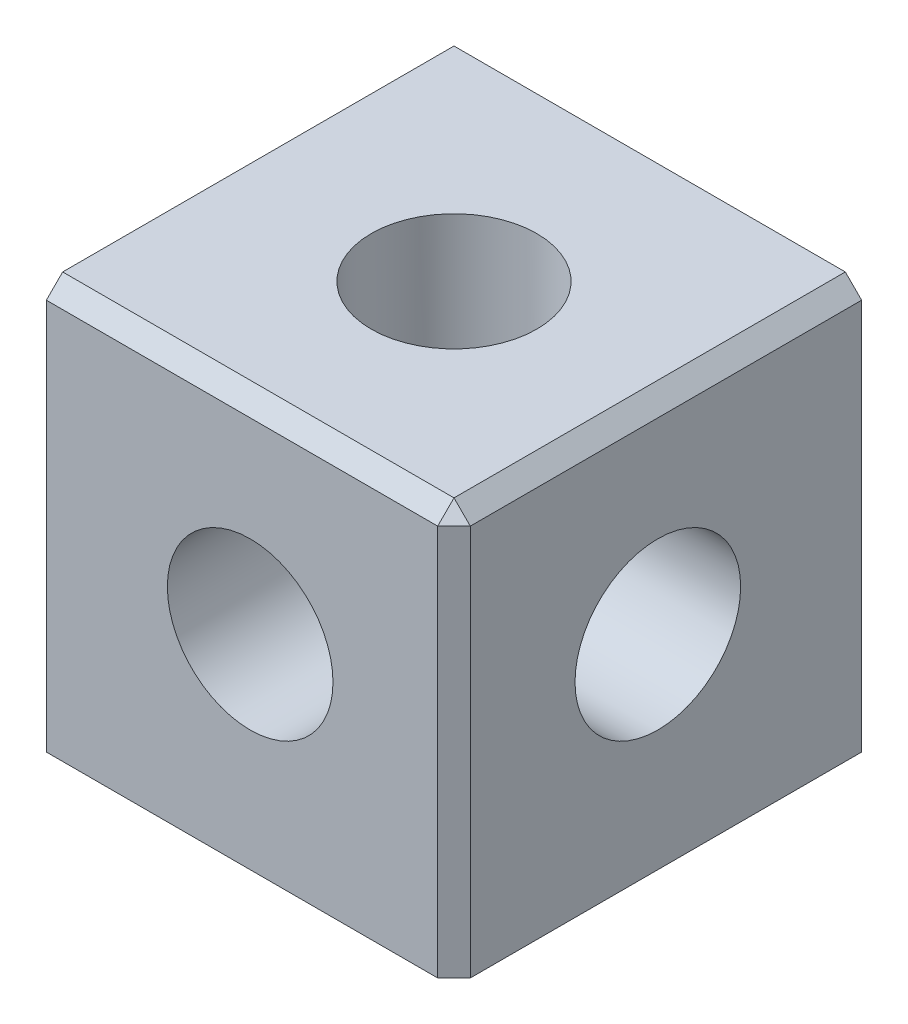
SolidWorks part; units mm, degrees
ref_plane "Front Plane" through (0, 0, 0) normal (0, 0, 1) x (1, 0, 0)
ref_plane "Top Plane" through (0, 0, 0) normal (0, 1, 0) x (1, 0, 0)
ref_plane "Right Plane" through (0, 0, 0) normal (1, 0, 0) x (0, 0, -1)
ref_plane "Plane1" through (0, 25.4, 0) normal (0, 1, 0) x (1, 0, 0)
sketch "Sketch1" plane through (0, 25.4, 0) normal (0, 1, 0) x (1, 0, 0)
  line L0 (-12.7, 12.7) -> (-12.7, -12.7)
  line L1 (-12.7, -12.7) -> (12.7, -12.7)
  line L2 (12.7, -12.7) -> (12.7, 12.7)
  line L3 (12.7, 12.7) -> (-12.7, 12.7)
extrude "Boss-Extrude1" add sketch "Sketch1" against normal blind 25.4
hole_wizard "Hole1" positions "Sketch3" profile "Sketch2" legacy
sketch "Sketch3" plane through (0, 0, 0) normal (0, -1, 0) x (-1, 0, 0)
  point P0 (0, 0)
sketch "Sketch2" plane through (0, 0, 0) normal (1, 0, 0) x (0, 0, -1)
  line L0 (0, 0) -> (0, 25.4)
  line L1 (0, 25.4) -> (5.16, 25.4)
  line L2 (5.16, 25.4) -> (5.16, 3.3)
  line L3 (5.16, 3.3) -> (3.26, 3.3)
  line L4 (3.26, 3.3) -> (3.26, 0)
  line L5 (3.26, 0) -> (0, 0)
  line L6 (0, 110) -> (0, -10) construction
  dimension "Diameter" = 10.32
  dimension "Depth" = 25.4
  dimension "C-Bore Diameter" = 6.52
  dimension "C-Bore Depth" = 3.3
hole_wizard "Hole2" positions "Sketch5" profile "Sketch4" legacy
sketch "Sketch5" plane through (0, 0, -12.7) normal (0, 0, -1) x (-1, 0, 0)
  point P0 (0, 12.7)
sketch "Sketch4" plane through (0, 12.7, -12.7) normal (1, 0, 0) x (0, 1, 0)
  line L0 (0, 0) -> (0, 12.7)
  line L1 (0, 12.7) -> (5.16, 12.7)
  line L2 (5.16, 12.7) -> (5.16, 3.3)
  line L3 (5.16, 3.3) -> (3.26, 3.3)
  line L4 (3.26, 3.3) -> (3.26, 0)
  line L5 (3.26, 0) -> (0, 0)
  line L6 (0, 110) -> (0, -10) construction
  dimension "Diameter" = 10.32
  dimension "Depth" = 12.7
  dimension "C-Bore Diameter" = 6.52
  dimension "C-Bore Depth" = 3.3
sketch "Sketch6" plane through (0, 0, -12.7) normal (0, 0, -1) x (-1, 0, 0)
  line L0 (12.7, 9.6) -> (9.73, 9.6)
  line L1 (9.73, 9.6) -> (9.73, 15.8)
  line L2 (9.73, 15.8) -> (12.7, 15.8)
  line L3 (12.7, 15.8) -> (12.7, 9.6)
extrude "Boss-Extrude2" add sketch "Sketch6" along normal blind 2.21
ref_plane "Plane2" through (-14.91, 0, 0) normal (-1, 0, 0) x (0, -1, 0)
sketch "Sketch7" plane through (-14.91, 0, 0) normal (-1, 0, 0) x (0, -1, 0)
  line L0 (-9.6, -12.7) -> (-9.6, -9.73)
  line L1 (-9.6, -9.73) -> (-15.8, -9.73)
  line L2 (-15.8, -9.73) -> (-15.8, -12.7)
  line L3 (-15.8, -12.7) -> (-9.6, -12.7)
extrude "Boss-Extrude3" add sketch "Sketch7" against normal up to next
sketch "Sketch8" plane through (0, 0, 0) normal (0, -1, 0) x (1, 0, 0)
  line L0 (-3.1, -12.7) -> (-3.1, -9.73)
  line L1 (-3.1, -9.73) -> (3.1, -9.73)
  line L2 (3.1, -9.73) -> (3.1, -12.7)
  line L3 (3.1, -12.7) -> (-3.1, -12.7)
extrude "Boss-Extrude4" add sketch "Sketch8" along normal blind 2.21
ref_plane "Plane3" through (0, 0, -14.91) normal (0, 0, -1) x (-1, 0, 0)
sketch "Sketch9" plane through (0, 0, -14.91) normal (0, 0, -1) x (-1, 0, 0)
  line L0 (3.1, 0) -> (3.1, 2.97)
  line L1 (3.1, 2.97) -> (-3.1, 2.97)
  line L2 (-3.1, 2.97) -> (-3.1, 0)
  line L3 (-3.1, 0) -> (3.1, 0)
extrude "Boss-Extrude5" add sketch "Sketch9" against normal up to next
sketch "Sketch10" plane through (0, 0, 0) normal (0, -1, 0) x (1, 0, 0)
  line L0 (-9.73, -3.1) -> (-12.7, -3.1)
  line L1 (-12.7, -3.1) -> (-12.7, 3.1)
  line L2 (-12.7, 3.1) -> (-9.73, 3.1)
  line L3 (-9.73, 3.1) -> (-9.73, -3.1)
extrude "Boss-Extrude6" add sketch "Sketch10" along normal blind 2.21
sketch "Sketch11" plane through (-14.91, 0, 0) normal (-1, 0, 0) x (0, -1, 0)
  line L0 (-2.97, -3.1) -> (0, -3.1)
  line L1 (0, -3.1) -> (0, 3.1)
  line L2 (0, 3.1) -> (-2.97, 3.1)
  line L3 (-2.97, 3.1) -> (-2.97, -3.1)
extrude "Boss-Extrude7" add sketch "Sketch11" against normal up to next
hole_wizard "Hole3" positions "Sketch13" profile "Sketch12" legacy
sketch "Sketch13" plane through (0, 0, 12.7) normal (0, 0, 1) x (1, 0, 0)
  point P0 (0, 12.7)
sketch "Sketch12" plane through (0, 12.7, 12.7) normal (1, 0, 0) x (0, -1, 0)
  line L0 (0, 0) -> (0, 7.54)
  line L1 (0, 7.54) -> (5.16, 7.54)
  line L2 (5.16, 7.54) -> (5.16, 0)
  line L3 (5.16, 0) -> (0, 0)
  line L4 (0, 110) -> (0, -10) construction
  dimension "Diameter" = 10.32
  dimension "Depth" = 7.54
hole_wizard "Hole4" positions "Sketch15" profile "Sketch14" legacy
sketch "Sketch15" plane through (12.7, 0, 0) normal (1, 0, 0) x (0, 0, -1)
  point P0 (0, 12.7)
sketch "Sketch14" plane through (12.7, 12.7, 0) normal (0, 1, 0) x (0, 0, -1)
  line L0 (0, 0) -> (0, 25.4)
  line L1 (0, 25.4) -> (3.26, 25.4)
  line L2 (3.26, 25.4) -> (3.26, 22.1)
  line L3 (3.26, 22.1) -> (5.16, 22.1)
  line L4 (5.16, 22.1) -> (5.16, 0)
  line L5 (5.16, 0) -> (0, 0)
  line L6 (0, 110) -> (0, -10) construction
  dimension "Diameter" = 6.52
  dimension "Depth" = 25.4
  dimension "C-Bore Diameter" = 10.32
  dimension "C-Bore Depth" = 22.1
chamfer "Chamfer1" distance 1.016 angle 45 3 edges at (12.7, 12.7, 12.7) (0, 25.4, 12.7) (12.7, 25.4, 0)
